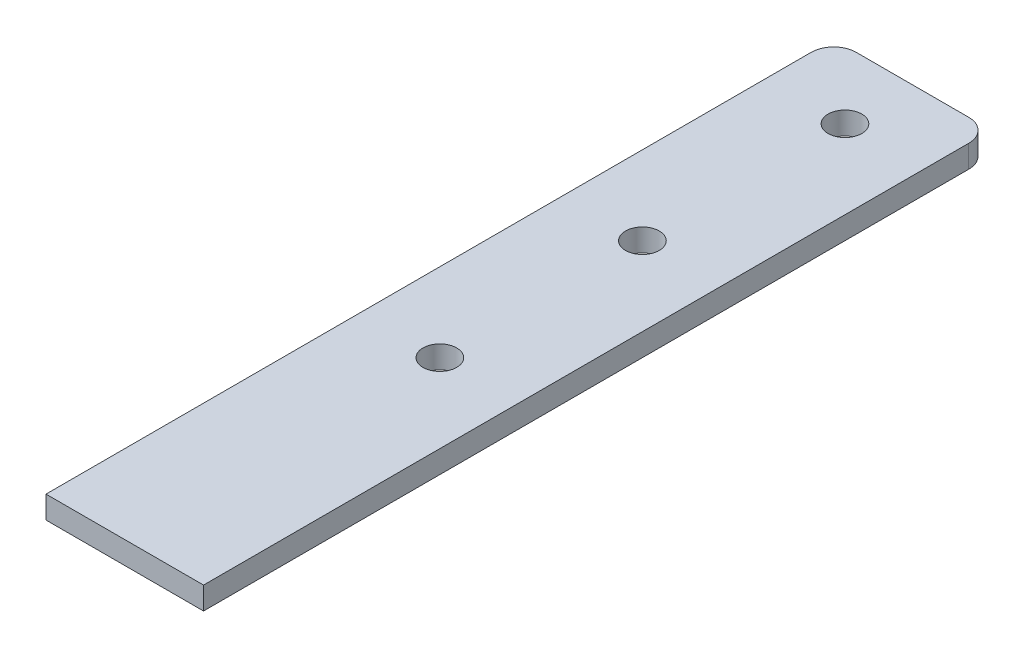
SolidWorks part; units mm, degrees
ref_plane "Alzado" through (0, 0, 0) normal (0, 0, 1) x (1, 0, 0)
ref_plane "Planta" through (0, 0, 0) normal (0, 1, 0) x (1, 0, 0)
ref_plane "Vista lateral" through (0, 0, 0) normal (1, 0, 0) x (0, 0, -1)
sketch "Croquis3" plane through (0, 0, 0) normal (0, 1, 0) x (1, 0, 0)
  line L0 (0, 175) -> (0, -175)
  line L1 (-35, -175) -> (35, -175)
  line L2 (-35, -175) -> (-35, 165)
  line L3 (-25, 175) -> (25, 175)
  line L4 (35, -175) -> (35, 165)
  line L5 (-35, -175) -> (35, 175) construction
  line L6 (-35, 175) -> (35, -175) construction
  arc A4 (25, 175) -> (35, 165) centre (25, 165) cw
  arc A5 (-25, 175) -> (-35, 165) centre (-25, 165) ccw
  circle A6 centre (0, 145) radius 7.5
  circle A7 centre (0, 55) radius 7.5
  circle A9 centre (0, -35) radius 7.5
  point P0 (0, 0)
  dimension "D1" = 15
  dimension "D3" = 15
  dimension "D4" = 30
  dimension "D6" = 10
  dimension "D2" = 15
  dimension "D5" = 90
  dimension "D7" = 70
  dimension "D8" = 90
  dimension "D9" = 350
extrude "Saliente-Extruir4" add sketch "Croquis3" along normal blind 10
